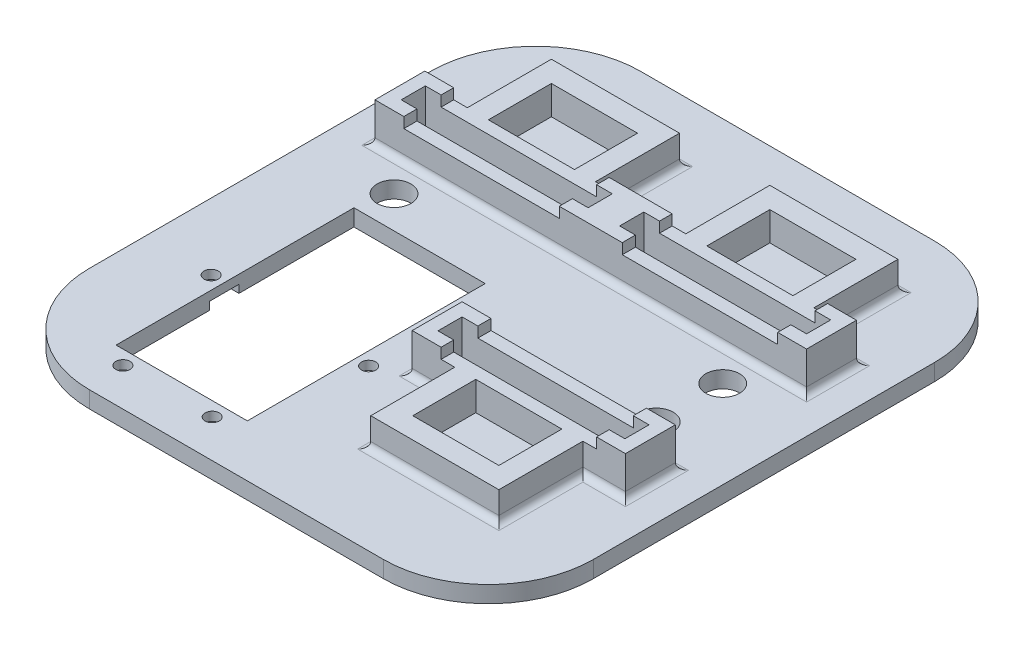
SolidWorks part; units mm, degrees
material "ABS"
ref_plane "Front Plane" through (0, 0, 0) normal (0, 0, 1) x (1, 0, 0)
ref_plane "Top Plane" through (0, 0, 0) normal (0, 1, 0) x (1, 0, 0)
ref_plane "Right Plane" through (0, 0, 0) normal (1, 0, 0) x (0, 0, -1)
sketch "Sketch1" plane through (0, 0, 0) normal (0, 1, 0) x (1, 0, 0)
  line L0 (-48, 0) -> (48, 0) construction
  line L1 (0, 50) -> (0, -55) construction
  line L2 (-38.6, 19.5) -> (-3, 19.5) construction
  line L3 (-38.6, 50.5) -> (-3, 50.5) construction
  line L4 (-38.6, 50.5) -> (-38.6, 15) construction
  line L5 (-38.6, 15) -> (-3, 15) construction
  line L6 (-38.6, 46) -> (-3, 46) construction
  line L7 (38.6, 15) -> (3, 50.5) construction
  line L8 (38.6, 50.5) -> (3, 15) construction
  line L9 (-3, 50.5) -> (-3, 15) construction
  line L10 (-38.6, 50.5) -> (-3, 15) construction
  line L11 (-38.6, 15) -> (-3, 50.5) construction
  line L12 (3, 50.5) -> (3, 15) construction
  line L13 (38.6, 46) -> (3, 46) construction
  line L14 (38.6, 15) -> (3, 15) construction
  line L15 (38.6, 50.5) -> (38.6, 15) construction
  line L16 (38.6, 50.5) -> (3, 50.5) construction
  line L17 (38.6, 19.5) -> (3, 19.5) construction
  line L18 (38.6, -19.5) -> (3, -19.5) construction
  line L19 (38.6, -50.5) -> (3, -50.5) construction
  line L20 (38.6, -50.5) -> (38.6, -15) construction
  line L21 (38.6, -15) -> (3, -15) construction
  line L22 (38.6, -46) -> (3, -46) construction
  line L23 (3, -50.5) -> (3, -15) construction
  line L24 (38.6, -50.5) -> (3, -15) construction
  line L25 (38.6, -15) -> (3, -50.5) construction
  line L26 (-38.1, 0) -> (-38.1, -50.6) construction
  line L27 (-38.1, -50.6) -> (-2.5, -50.6) construction
  line L28 (-2.5, -50.6) -> (-2.5, 0) construction
  line L29 (-2.5, 0) -> (-38.1, 0) construction
  line L30 (-48, -35) -> (-48, 30)
  line L31 (-28, 50) -> (28, 50)
  line L32 (48, 30) -> (48, -35)
  line L33 (28, -55) -> (-28, -55)
  line L34 (20.8, -50.5) -> (20.8, -15) construction
  line L35 (20.8, 15) -> (20.8, 50.5) construction
  line L36 (-20.8, 15) -> (-20.8, 50.5) construction
  line L37 (-33.38, 15) -> (-33.38, 6.08) construction
  line L38 (-33.38, 6.08) -> (-8.22, 6.08) construction
  line L39 (-8.22, 6.08) -> (-8.22, 15) construction
  line L40 (8.22, 6.08) -> (8.22, 15) construction
  line L41 (33.38, 6.08) -> (8.22, 6.08) construction
  line L42 (33.38, 15) -> (33.38, 6.08) construction
  line L43 (33.38, -15) -> (33.38, -6.08) construction
  line L44 (33.38, -6.08) -> (8.22, -6.08) construction
  line L45 (8.22, -6.08) -> (8.22, -15) construction
  arc A0 (48, -35) -> (28, -55) centre (28, -35) cw
  arc A1 (48, 30) -> (28, 50) centre (28, 30) ccw
  arc A2 (-48, 30) -> (-28, 50) centre (-28, 30) cw
  arc A3 (-28, -55) -> (-48, -35) centre (-28, -35) cw
  point P8 (-20.8, 32.75)
  point P21 (20.8, 32.75)
  point P30 (20.8, -32.75)
  dimension "D1" = 35.6
  dimension "D14" = 20
  dimension "D2" = 35.5
  dimension "D3" = 4.5
  dimension "D4" = 3
  dimension "D5" = 35.6
  dimension "D6" = 50.6
  dimension "D7" = 15
  dimension "D8" = 4.5
  dimension "D9" = 2.5
  dimension "D10" = 48
  dimension "D11" = 48
  dimension "D12" = 50
  dimension "D13" = 55
  dimension "D15" = 8.92
  dimension "D16" = 25.16
  dimension "D17" = 12.58
extrude "w_top" add sketch "Sketch1" along normal blind 3.175
extrude "a_holders" add sketch "Sketch3" along normal blind 5.5 from surface at 0 starting at face at (0, 3.175, 2.5)
sketch "Sketch3" plane through (0, 3.175, 0) normal (0, 1, 0) x (1, 0, 0)
  line L0 (20.8, 15) -> (20.8, 38) construction
  line L1 (-20.8, 15) -> (-20.8, 50.5) construction
  line L2 (-48, 0) -> (48, 0) construction
  line L3 (0, 50) -> (0, -55) construction
  line L7 (-38.6, 19.6) -> (-38.6, 15) construction
  line L8 (3, 15) -> (38.6, 15)
  line L9 (-3, 19.6) -> (-38.6, 19.6)
  line L10 (-29, 22) -> (-29, 34)
  line L11 (-33, 22) -> (-33, 38)
  line L12 (-20.8, 38) -> (-20.8, 12.5) construction
  line L13 (-33, 38) -> (-8.6, 38)
  line L14 (3, 15) -> (3, 19.6)
  line L15 (-3, 15) -> (-3, 19.6)
  line L16 (-38.6, 19.6) -> (-38.6, 15)
  line L17 (38.6, 19.6) -> (3, 19.6)
  line L18 (38.6, 15) -> (38.6, 19.6)
  line L19 (8.6, -22) -> (0.5, -22)
  line L20 (3, -15) -> (3, -19.6)
  line L21 (38.6, -19.6) -> (3, -19.6)
  line L22 (38.6, -15) -> (38.6, -19.6)
  line L23 (-8.6, 38) -> (-8.6, 22)
  line L24 (3, -15) -> (38.6, -15)
  line L25 (-29, 34) -> (-12.6, 34)
  line L26 (-12.6, 34) -> (-12.6, 22)
  line L27 (0.5, -12.5) -> (41.1, -12.5)
  line L28 (41.1, -12.5) -> (41.1, -22)
  line L29 (41.1, -22) -> (33, -22)
  line L30 (20.8, -15) -> (20.8, -38) construction
  line L31 (33, -38) -> (33, -22)
  line L32 (8.6, -38) -> (33, -38)
  line L33 (8.6, 22) -> (8.6, 38)
  line L34 (8.6, 38) -> (33, 38)
  line L35 (33, 38) -> (33, 22)
  line L36 (-38.6, 15) -> (-3, 15)
  line L37 (8.6, -22) -> (8.6, -38)
  line L38 (0.5, -22) -> (0.5, -12.5)
  line L39 (3, -17.3) -> (38.6, -17.3) construction
  line L40 (48, 30) -> (48, -35) construction
  line L41 (28, -55) -> (-28, -55) construction
  line L42 (-41.1, 22) -> (-41.1, 12.5)
  line L43 (12.6, 22) -> (12.6, 34)
  line L44 (41.1, 22) -> (33, 22)
  line L45 (41.1, 12.5) -> (41.1, 22)
  line L46 (-41.1, 12.5) -> (41.1, 12.5)
  line L47 (-41.1, 17.25) -> (41.1, 17.25) construction
  line L48 (12.6, 34) -> (29, 34)
  line L49 (29, 34) -> (29, 22)
  line L50 (-29, 22) -> (-12.6, 22)
  line L51 (-33, 22) -> (-41.1, 22)
  line L52 (12.6, 22) -> (29, 22)
  line L53 (8.6, 22) -> (-8.6, 22)
  line L54 (12.6, -22) -> (12.6, -34)
  line L55 (12.6, -34) -> (29, -34)
  line L56 (29, -34) -> (29, -22)
  line L57 (12.6, -22) -> (29, -22)
  point P0 (-38.6, 50.5)
  point P1 (49.6897, 50.5)
  point P3 (49.6897, 45.9)
  point P4 (-38.6, 45.9)
  dimension "D4" = 35.6
  dimension "D1" = 4.6
  dimension "D2" = 9.5
  dimension "D3" = 82.2
  dimension "D5" = 24.4
  dimension "D6" = 9.5
  dimension "D7" = 16
  dimension "D8" = 0.5
  dimension "D9" = 12.5
  dimension "D10" = 2.5
  dimension "D11" = 2.5
  dimension "D12" = 40.6
  dimension "D13" = 16
  dimension "D14" = 6
  dimension "D15" = 2.5
  dimension "D16" = 8.1
  dimension "D18" = 4
  dimension "D17" = 4
fillet "holder_chamfer" radius 1.25 20 edges at (37.05, 3.175, 22) (41.1, 3.175, -17.25) (37.05, 3.175, -22) (-41.1, 3.175, -17.25) (0, 3.175, -12.5) (-20.8, 3.175, -38) (-37.05, 3.175, -22) (-33, 3.175, -30) (33, 3.175, -30) (0, 3.175, -22) (20.8, 3.175, -38) (8.6, 3.175, -30) (-8.6, 3.175, -30) (0.5, 3.175, 17.25) (4.55, 3.175, 22) (8.6, 3.175, 30) (20.8, 3.175, 38) (33, 3.175, 30) (41.1, 3.175, 17.25) (20.8, 3.175, 12.5)
sketch "Sketch14" plane through (0, 8.675, 0) normal (0, 1, 0) x (1, 0, 0)
  line L0 (-35.6, 19.6) -> (-35.6, 22)
  line L1 (-38.6, 19.6) -> (-3, 19.6) construction
  line L2 (-41.1, 22) -> (-33, 22) construction
  line L3 (-35.6, 22) -> (-41.1, 22)
  line L4 (-41.1, 22) -> (-41.1, 12.5)
  line L5 (-41.1, 12.5) -> (-35.6, 12.5)
  line L6 (41.1, 12.5) -> (-41.1, 12.5) construction
  line L7 (-35.6, 12.5) -> (-35.6, 15)
  line L8 (-3, 15) -> (-38.6, 15) construction
  line L9 (-35.6, 15) -> (-38.6, 15)
  line L10 (-38.6, 15) -> (-38.6, 19.6)
  line L11 (-38.6, 19.6) -> (-35.6, 19.6)
  line L12 (0, 0) -> (0, 50) construction
  line L13 (-28, 50) -> (28, 50) construction
  line L14 (0, 0) -> (48, 0) construction
  line L15 (48, 30) -> (48, -35) construction
  line L16 (-20.8, 15) -> (-20.8, 38) construction
  line L17 (-3, 15) -> (-38.6, 15) construction
  line L18 (-33, 38) -> (-8.6, 38) construction
  line L19 (-3, 19.6) -> (-6, 19.6)
  line L20 (-3, 15) -> (-3, 19.6)
  line L21 (-6, 15) -> (-3, 15)
  line L22 (-6, 12.5) -> (-6, 15)
  line L23 (-6, 22) -> (6, 22)
  line L24 (-6, 12.5) -> (6, 12.5)
  line L26 (-6, 19.6) -> (-6, 22)
  line L27 (6, 19.6) -> (6, 22)
  line L31 (6, 12.5) -> (6, 15)
  line L32 (6, 15) -> (3, 15)
  line L33 (3, 15) -> (3, 19.6)
  line L34 (3, 19.6) -> (6, 19.6)
  line L35 (38.6, 19.6) -> (35.6, 19.6)
  line L36 (38.6, 15) -> (38.6, 19.6)
  line L37 (35.6, 15) -> (38.6, 15)
  line L38 (35.6, 12.5) -> (35.6, 15)
  line L39 (41.1, 12.5) -> (35.6, 12.5)
  line L40 (41.1, 22) -> (41.1, 12.5)
  line L41 (35.6, 22) -> (41.1, 22)
  line L42 (35.6, 19.6) -> (35.6, 22)
  line L43 (0.5, -12.5) -> (6, -12.5)
  line L44 (0.5, -22) -> (0.5, -12.5)
  line L45 (6, -22) -> (0.5, -22)
  line L46 (35.6, -19.6) -> (35.6, -22)
  line L47 (35.6, -22) -> (41.1, -22)
  line L48 (41.1, -22) -> (41.1, -12.5)
  line L49 (41.1, -12.5) -> (35.6, -12.5)
  line L50 (35.6, -12.5) -> (35.6, -15)
  line L51 (35.6, -15) -> (38.6, -15)
  line L52 (38.6, -15) -> (38.6, -19.6)
  line L53 (38.6, -19.6) -> (35.6, -19.6)
  line L54 (3, -19.6) -> (6, -19.6)
  line L55 (3, -15) -> (3, -19.6)
  line L56 (6, -15) -> (3, -15)
  line L57 (6, -12.5) -> (6, -15)
  line L58 (6, -19.6) -> (6, -22)
  dimension "D1" = 5.5
extrude "a_clamp" add sketch "Sketch14" along normal blind 2
sketch "Sketch12" plane through (0, 3.175, 0) normal (0, 1, 0) x (1, 0, 0)
  line L0 (-38.1, 0) -> (-2.5, 0) construction
  line L1 (-2.5, 0) -> (-2.5, -50.6) construction
  line L2 (-2.5, -50.6) -> (-38.1, -50.6) construction
  line L3 (-38.1, -50.6) -> (-38.1, 0) construction
  line L4 (-20.3, 0) -> (-20.3, -50.6) construction
  line L5 (-38.1, -12) -> (-2.5, -12) construction
  line L6 (-32.5, 0) -> (-32.5, -45) construction
  line L7 (-8.1, 0) -> (-8.1, -45) construction
  line L8 (-32.5, -45) -> (-8.1, -45) construction
  line L9 (-35.3, -47.8) -> (-5.3, -47.8) construction
  line L10 (-35.3, -47.8) -> (-35.3, 0) construction
  line L11 (-5.3, 0) -> (-5.3, -47.8) construction
  line L12 (-35.3, -24.5) -> (-5.3, -24.5) construction
  line L13 (-32.8, 0.2) -> (-32.8, -45.1)
  line L14 (-32.8, -45.1) -> (-7.8, -45.1)
  line L15 (-7.8, -45.1) -> (-7.8, 0.2)
  line L16 (-32.8, 0.2) -> (-7.8, 0.2)
  circle A0 centre (-20.3, -12) radius 11 construction
  circle A1 centre (-28.8, -47.8) radius 1.35
  circle A2 centre (-11.8, -47.8) radius 1.35
  circle A4 centre (-35.3, -24.5) radius 1.35
  circle A5 centre (-5.3, -24.5) radius 1.35
  dimension "D1" = 12
  dimension "D2" = 22
  dimension "D9" = 2.7
  dimension "D10" = 8.5
  dimension "D11" = 8.5
  dimension "D12" = 12.5
  dimension "D13" = 0.3
  dimension "D14" = 0.3
  dimension "D3" = 5.6
  dimension "D4" = 5.6
  dimension "D5" = 5.6
  dimension "D6" = 35.8
  dimension "D7" = 2.8
  dimension "D8" = 2.8
  dimension "D15" = 0.2
  dimension "D16" = 0.2
extrude "a_holes" cut sketch "Sketch12" against normal up to surface (3.175 mm away) up to face at (0, 0, 2.5)
sketch "Sketch13" plane through (0, 0, 0) normal (0, -1, 0) x (1, 0, 0)
  line L0 (-31.6, 47.8) -> (-31.6, 45.1)
  line L1 (-7.8, 45.1) -> (-32.8, 45.1) construction
  line L3 (-31.6, 45.1) -> (-26, 45.1)
  line L4 (-26, 45.1) -> (-26, 47.8)
  line L5 (-35.3, 27.3) -> (-32.8, 27.3)
  line L7 (-32.8, 27.3) -> (-32.8, 21.7)
  line L8 (-32.8, 21.7) -> (-35.3, 21.7)
  line L9 (-20.3, 45.1) -> (-20.3, -0.2) construction
  line L11 (-7.8, 21.7) -> (-5.3, 21.7)
  line L12 (-7.8, 27.3) -> (-7.8, 21.7)
  line L13 (-5.3, 27.3) -> (-7.8, 27.3)
  line L14 (-14.6, 45.1) -> (-14.6, 47.8)
  line L15 (-9, 45.1) -> (-14.6, 45.1)
  line L16 (-9, 47.8) -> (-9, 45.1)
  line L17 (-32.8, 45.1) -> (-32.8, -0.2) construction
  line L18 (-32.8, -0.2) -> (-7.8, -0.2) construction
  arc A0 (-26, 47.8) -> (-31.6, 47.8) centre (-28.8, 47.8) ccw
  arc A1 (-5.3, 27.3) -> (-5.3, 21.7) centre (-5.3, 24.5) cw
  arc A2 (-14.6, 47.8) -> (-9, 47.8) centre (-11.8, 47.8) cw
  arc A3 (-35.3, 27.3) -> (-35.3, 21.7) centre (-35.3, 24.5) ccw
extrude "a_holes guide" cut sketch "Sketch13" against normal blind 1.5
sketch "Sketch15" plane through (0, 3.175, 0) normal (0, 1, 0) x (1, 0, 0)
  line L0 (-38.35, 12.5) -> (-38.35, 6.33) construction
  line L1 (-41.1, 12.5) -> (-35.6, 12.5) construction
  line L2 (-38.35, 6.33) -> (-3, 6.33) construction
  line L3 (-3, 6.33) -> (-3, 12.5) construction
  line L4 (-38.35, 12.5) -> (-3, 12.5) construction
  line L5 (-41.1, 12.5) -> (41.1, 12.5) construction
  line L6 (-35.6, 12.5) -> (-35.6, 15) construction
  line L7 (6, 12.5) -> (6, 15) construction
  line L8 (20.8, 15) -> (20.8, 38) construction
  line L9 (-3, 19.6) -> (-3, 15) construction
  line L10 (0, 0) -> (0, 50) construction
  line L11 (-28, 50) -> (28, 50) construction
  line L12 (0, 0) -> (48, 0) construction
  line L13 (48, 30) -> (48, -35) construction
  line L14 (38.35, 12.5) -> (3, 12.5) construction
  line L15 (3, 6.33) -> (3, 12.5) construction
  line L16 (38.35, 6.33) -> (3, 6.33) construction
  line L17 (38.35, 12.5) -> (38.35, 6.33) construction
  line L18 (38.35, -12.5) -> (38.35, -6.33) construction
  line L19 (38.35, -6.33) -> (3, -6.33) construction
  line L20 (3, -6.33) -> (3, -12.5) construction
  line L21 (38.35, -12.5) -> (3, -12.5) construction
  line L22 (38.6, 15) -> (3, 15) construction
  line L23 (8.6, 38) -> (33, 38) construction
  line L24 (-20.675, 12.5) -> (-20.675, 6.33) construction
  line L25 (20.675, -6.33) -> (20.675, -12.5) construction
  circle A0 centre (-31.3, 6.33) radius 3.225
  circle A1 centre (10.3, 6.33) radius 3.225 construction
  circle A2 centre (31.3, 6.33) radius 3.225
  circle A3 centre (31.3, -6.33) radius 3.225
  circle A4 centre (10.05, -6.33) radius 3.225 construction
  dimension "D2" = 6.45
  dimension "D3" = 4.3
  dimension "D4" = 4.3
  dimension "D1" = 6.17
extrude "tendon holes" cut sketch "Sketch15" against normal up to surface (3.175 mm away) up to face at (-20.3, 0, 33.15)
